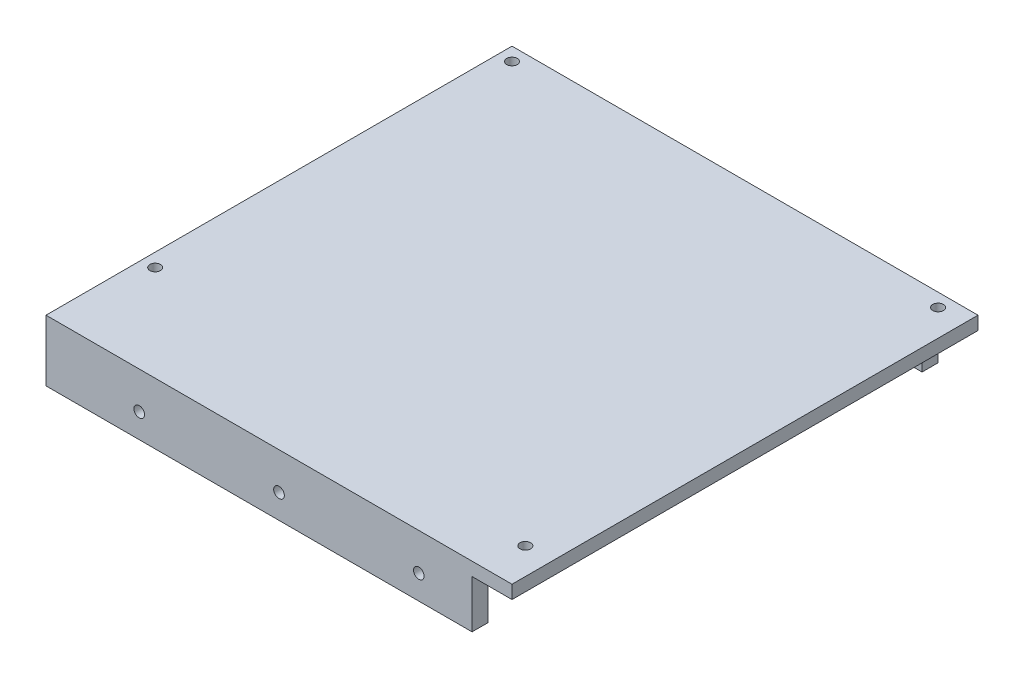
SolidWorks part; units mm, degrees
ref_plane "Front Plane" through (0, 0, 0) normal (0, 0, 1) x (1, 0, 0)
ref_plane "Top Plane" through (0, 0, 0) normal (0, 1, 0) x (1, 0, 0)
ref_plane "Right Plane" through (0, 0, 0) normal (1, 0, 0) x (0, 0, -1)
sketch "Sketch1" plane through (0, 0, 0) normal (0, 1, 0) x (1, 0, 0)
  line L1 (-111.5458, 60.1145) -> (63.4542, 60.1145)
  line L2 (-111.5458, 60.1145) -> (-111.5458, -114.8855)
  line L3 (-111.5458, -114.8855) -> (63.4542, -114.8855)
  line L4 (63.4542, 60.1145) -> (63.4542, -114.8855)
  dimension "D1" = 175
  dimension "D2" = 175
extrude "Boss-Extrude1" add sketch "Sketch1" along normal blind 5
sketch "Sketch2" plane through (0, 5, 0) normal (0, 1, 0) x (1, 0, 0)
  line L0 (-111.5458, 60.1145) -> (-111.5458, -114.8855) construction
  line L1 (63.4542, 60.1145) -> (-111.5458, 60.1145) construction
  line L2 (63.4542, -114.8855) -> (63.4542, 60.1145) construction
  line L3 (-111.5458, -114.8855) -> (63.4542, -114.8855) construction
  circle A0 centre (-106.5458, 55.1145) radius 2
  circle A1 centre (53.4542, 55.1145) radius 2
  circle A2 centre (53.4542, -99.8855) radius 2
  circle A3 centre (-106.5458, -78.8855) radius 2
  dimension "D1" = 5
  dimension "D3" = 10
  dimension "D5" = 15
  dimension "D6" = 36
  dimension "D2" = 5
  dimension "D4" = 5
  dimension "D7" = 10
extrude "Cut-Extrude1" cut sketch "Sketch2" against normal blind 5
sketch "Sketch3" plane through (0, 0, 0) normal (0, -1, 0) x (1, 0, 0)
  line L0 (63.4542, -60.1145) -> (-111.5458, -60.1145) construction
  line L1 (-111.5458, 114.8855) -> (48.4542, 114.8855)
  line L2 (-111.5458, 114.8855) -> (-111.5458, 108.8855)
  line L3 (-111.5458, 108.8855) -> (48.4542, 108.8855)
  line L4 (48.4542, 114.8855) -> (48.4542, 108.8855)
  line L5 (-96.5458, -60.1145) -> (48.4542, -60.1145)
  line L6 (-96.5458, -60.1145) -> (-96.5458, -54.1145)
  line L7 (-96.5458, -54.1145) -> (48.4542, -54.1145)
  line L8 (48.4542, -60.1145) -> (48.4542, -54.1145)
  line L9 (-111.5458, -60.1145) -> (-111.5458, 114.8855) construction
  line L10 (63.4542, 114.8855) -> (63.4542, -60.1145) construction
  dimension "D1" = 6
  dimension "D2" = 160
  dimension "D3" = 6
  dimension "D4" = 15
  dimension "D5" = 15
extrude "Boss-Extrude3" add sketch "Sketch3" along normal blind 18
sketch "Sketch4" plane through (0, 0, -60.1145) normal (0, 0, -1) x (-1, 0, 0)
  line L0 (-48.4542, -18) -> (-48.4542, 0) construction
  line L1 (96.5458, -18) -> (96.5458, 0) construction
  circle A0 centre (-28.4542, -8.9008) radius 2
  circle A1 centre (24.0458, -8.9008) radius 2
  circle A2 centre (76.5458, -8.9008) radius 2
  dimension "D1" = 20
  dimension "D2" = 20
  dimension "D3" = 52.5
extrude "Cut-Extrude2" cut sketch "Sketch4" against normal through all both and the other way through all
sketch "Sketch5" plane through (0, 0, -60.1145) normal (0, 0, -1) x (-1, 0, 0)
  circle A0 centre (-28.4542, -8.9008) radius 5
  circle A1 centre (24.0458, -8.9008) radius 5
  circle A2 centre (76.5458, -8.9008) radius 5
extrude "Cut-Extrude3" cut sketch "Sketch5" against normal blind 2.5
